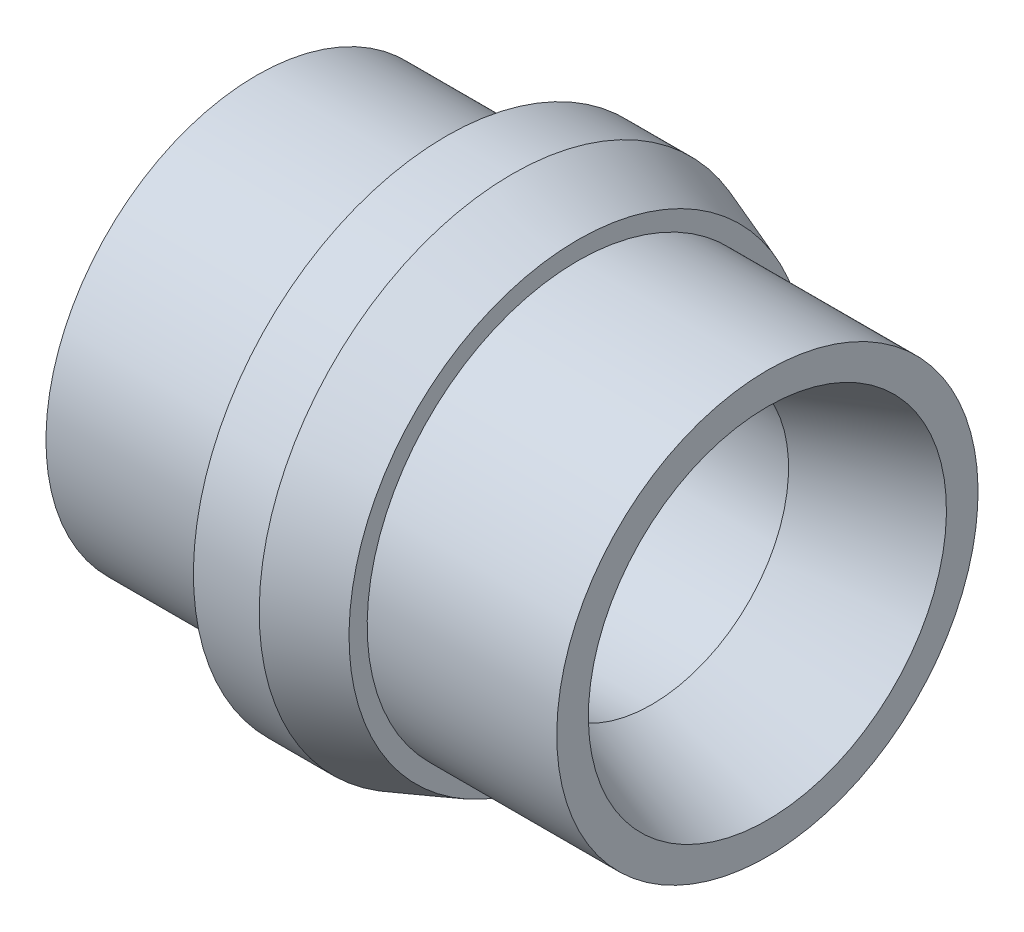
SolidWorks part; units mm, degrees
material "ABS PC"
ref_plane "Front Plane" through (0, 0, 0) normal (0, 0, 1) x (1, 0, 0)
ref_plane "Top Plane" through (0, 0, 0) normal (0, 1, 0) x (1, 0, 0)
ref_plane "Right Plane" through (0, 0, 0) normal (1, 0, 0) x (0, 0, -1)
sketch "Sketch1" plane through (0, 0, 0) normal (0, 0, 1) x (1, 0, 0)
  line L1 (0, 6.096) -> (1.5875, 6.096)
  line L2 (1.5875, 6.096) -> (3.175, 5.5182)
  line L3 (3.175, 5.5182) -> (3.175, 5.08)
  line L4 (3.175, 5.08) -> (7.747, 5.08)
  line L5 (7.747, 5.08) -> (7.747, 4.318)
  line L9 (3.8689, 0) -> (0, 0) construction
  line L11 (-4.572, 3.302) -> (4.9556, 3.302)
  line L12 (4.9556, 3.302) -> (7.747, 4.318)
  line L14 (-4.572, 3.302) -> (-4.572, 5.08)
  line L15 (-4.572, 5.08) -> (0, 5.08)
  line L16 (0, 5.08) -> (0, 6.096)
  dimension "D1" = 6.096
  dimension "D2" = 3.302
  dimension "D3" = 4.572
  dimension "D4" = 3.175
  dimension "D5" = 1.5875
  dimension "D6" = 20
  dimension "D7" = 5.08
  dimension "D8" = 20
  dimension "D9" = 1.016
revolve "Revolve1" add sketch "Sketch1" angle 360 about L9
move or copy body "Body-Move/Copy1" [suppressed] bodies to move or copy 101 parameters "D1"=0, "D2"=0, "D3"=0
move or copy body "Body-Move/Copy2" [suppressed] bodies to move or copy 102 parameters "D1"=0, "D2"=0, "D3"=0
move or copy body "Body-Move/Copy3" [suppressed] bodies to move or copy 103 parameters "D1"=0, "D2"=0, "D3"=0
